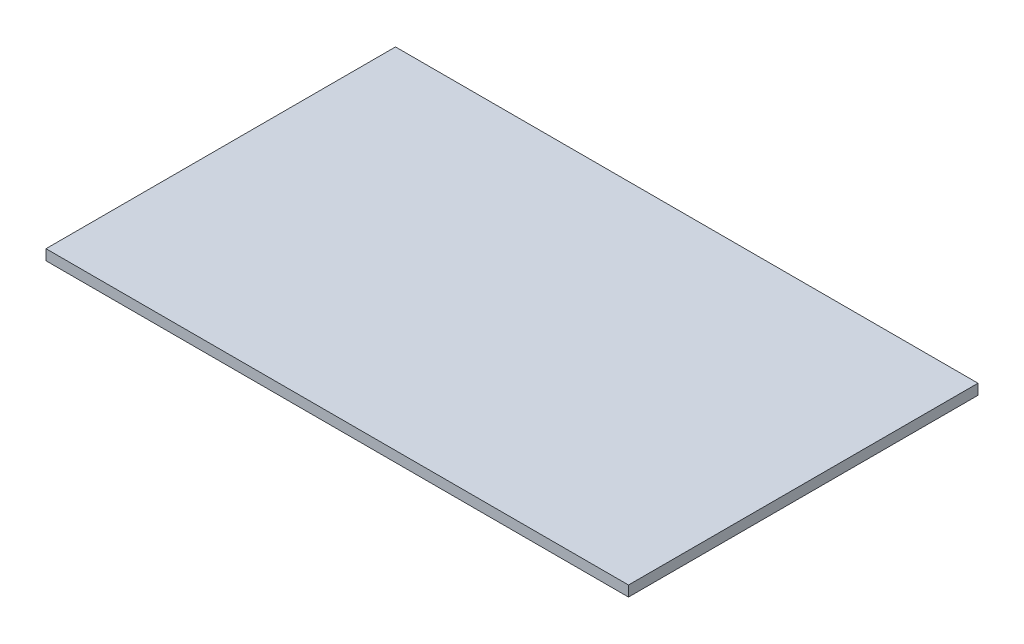
SolidWorks part; units mm, degrees
ref_plane "Спереди" through (0, 0, 0) normal (0, 0, 1) x (1, 0, 0)
ref_plane "Сверху" through (0, 0, 0) normal (0, 1, 0) x (1, 0, 0)
ref_plane "Справа" through (0, 0, 0) normal (1, 0, 0) x (0, 0, -1)
sketch "Эскиз1" plane through (0, 0, 0) normal (0, 1, 0) x (1, 0, 0)
  line L1 (0, 0) -> (1000, 0)
  line L2 (0, 0) -> (0, 600)
  line L3 (0, 600) -> (1000, 600)
  line L4 (1000, 0) -> (1000, 600)
  dimension "D1" = 600
  dimension "D2" = 1000
extrude "Бобышка-Вытянуть1" add sketch "Эскиз1" along normal blind 18
